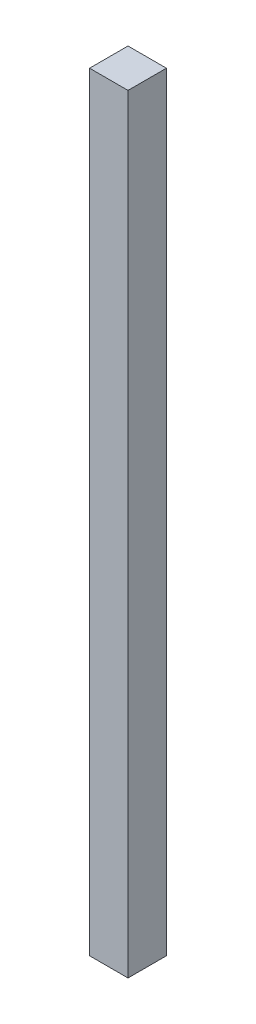
SolidWorks part; units mm, degrees
ref_plane "Front Plane" through (0, 0, 0) normal (0, 0, 1) x (1, 0, 0)
ref_plane "Top Plane" through (0, 0, 0) normal (0, 1, 0) x (1, 0, 0)
ref_plane "Right Plane" through (0, 0, 0) normal (1, 0, 0) x (0, 0, -1)
sketch "Sketch1" plane through (0, 0, 0) normal (0, 1, 0) x (1, 0, 0)
  line L1 (-20, -20) -> (20, -20)
  line L2 (-20, -20) -> (-20, 20)
  line L3 (-20, 20) -> (20, 20)
  line L4 (20, -20) -> (20, 20)
  line L5 (-20, -20) -> (20, 20) construction
  line L6 (-20, 20) -> (20, -20) construction
  point P0 (0, 0)
  dimension "D1" = 40
extrude "Boss-Extrude1" add sketch "Sketch1" along normal blind 800
